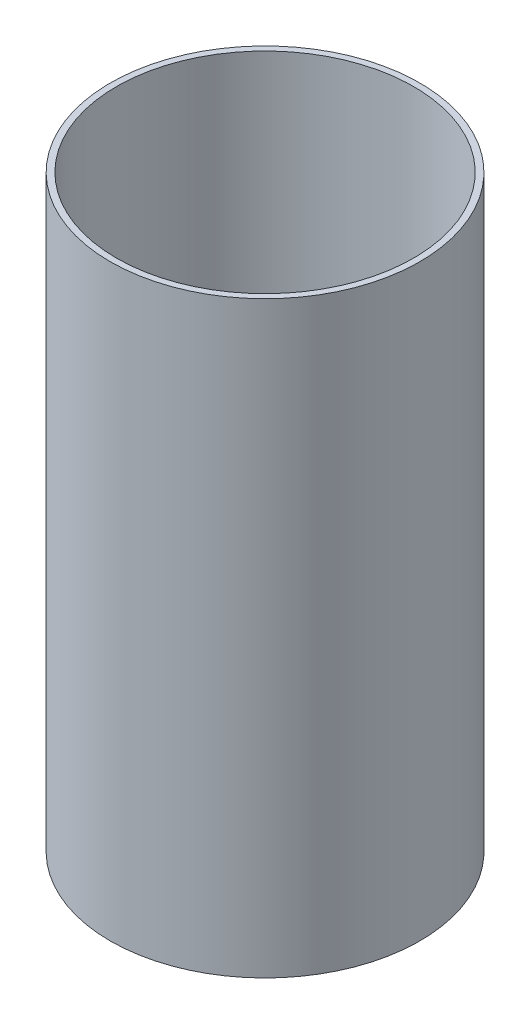
SolidWorks part; units mm, degrees
ref_plane "Front Plane" through (0, 0, 0) normal (0, 0, 1) x (1, 0, 0)
ref_plane "Top Plane" through (0, 0, 0) normal (0, 1, 0) x (1, 0, 0)
ref_plane "Right Plane" through (0, 0, 0) normal (1, 0, 0) x (0, 0, -1)
sketch "Sketch1" plane through (0, 0, 0) normal (0, 1, 0) x (1, 0, 0)
  circle A0 centre (0, 0) radius 38.1
  circle A1 centre (0, 0) radius 36.576
  dimension "D1" = 76.2
  dimension "D2" = 73.152
extrude "Boss-Extrude1" add sketch "Sketch1" along normal mid plane 144.78
